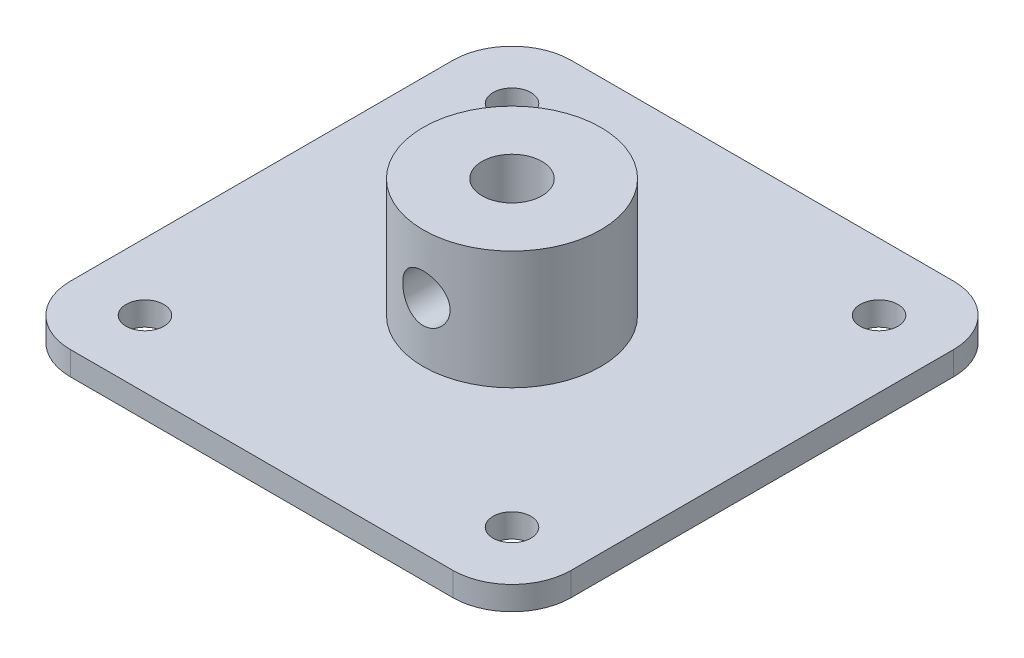
SolidWorks part; units mm, degrees
ref_plane "前视基准面" through (0, 0, 0) normal (0, 0, 1) x (1, 0, 0)
ref_plane "上视基准面" through (0, 0, 0) normal (0, 1, 0) x (1, 0, 0)
ref_plane "右视基准面" through (0, 0, 0) normal (1, 0, 0) x (0, 0, -1)
sketch "草图1" plane through (0, 0, 0) normal (0, 1, 0) x (1, 0, 0)
  line L1 (-21.15, 21.15) -> (21.15, 21.15)
  line L2 (-21.15, 21.15) -> (-21.15, -21.15)
  line L3 (-21.15, -21.15) -> (21.15, -21.15)
  line L4 (21.15, 21.15) -> (21.15, -21.15)
  line L5 (-21.15, 21.15) -> (21.15, -21.15) construction
  line L6 (-21.15, -21.15) -> (21.15, 21.15) construction
  point P0 (0, 0)
  dimension "D1" = 42.3
  dimension "D2" = 42.3
extrude "凸台-拉伸1" add sketch "草图1" along normal blind 2
sketch "草图2" plane through (0, 2, 0) normal (0, 1, 0) x (1, 0, 0)
  line L0 (0, 0) -> (0, 22.8528) construction
  line L1 (0, 0) -> (30.3517, 0) construction
  circle A0 centre (-15.5, 15.5) radius 1.6
  circle A1 centre (15.5, 15.5) radius 1.6
  circle A2 centre (15.5, -15.5) radius 1.6
  circle A3 centre (-15.5, -15.5) radius 1.6
  dimension "D3" = 3.2
  dimension "D1" = 31
  dimension "D2" = 31
extrude "切除-拉伸1" cut sketch "草图2" against normal through all
sketch "草图3" plane through (0, 2, 0) normal (0, 1, 0) x (1, 0, 0)
  circle A0 centre (0, 0) radius 7.5
  dimension "D1" = 15
extrude "凸台-拉伸2" add sketch "草图3" along normal blind 10
sketch "草图4" plane through (0, 12, 0) normal (0, 1, 0) x (1, 0, 0)
  circle A0 centre (0, 0) radius 2.525
  dimension "D1" = 5.05
extrude "切除-拉伸3" cut sketch "草图4" against normal through all
fillet "圆角1" radius 5 4 edges at (21.15, 1, -21.15) (21.15, 1, 21.15) (-21.15, 1, 21.15) (-21.15, 1, -21.15)
ref_plane "基准面1" through (0, 0, 7.5) normal (0, 0, 1) x (1, 0, 0)
sketch "草图5" plane through (0, 0, 7.5) normal (0, 0, 1) x (1, 0, 0)
  line L0 (7.5, 12) -> (-7.5, 12) construction
  circle A0 centre (0, 7) radius 2
  dimension "D1" = 4
  dimension "D2" = 5
extrude "切除-拉伸4" cut sketch "草图5" against normal up to next
